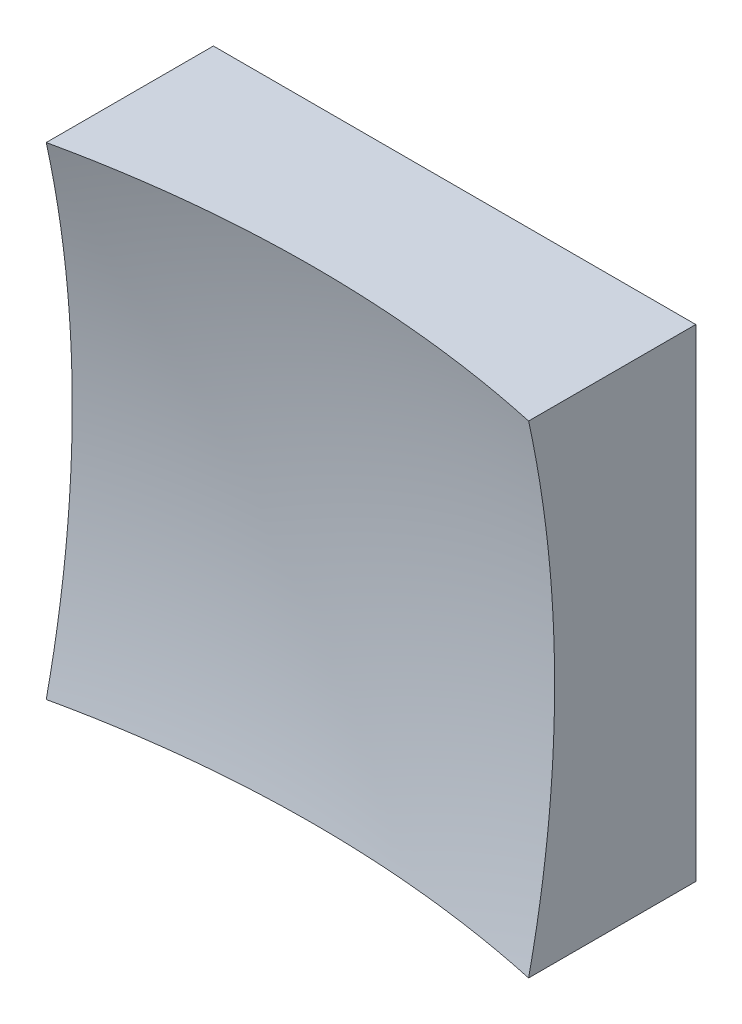
SolidWorks part; units mm, degrees
ref_plane "前视基准面" through (0, 0, 0) normal (0, 0, 1) x (1, 0, 0)
ref_plane "上视基准面" through (0, 0, 0) normal (0, 1, 0) x (1, 0, 0)
ref_plane "右视基准面" through (0, 0, 0) normal (1, 0, 0) x (0, 0, -1)
sketch "草图1" plane through (0, 0, 0) normal (0, 0, 1) x (1, 0, 0)
  line L1 (-6.25, 6.25) -> (6.25, 6.25)
  line L2 (-6.25, 6.25) -> (-6.25, -6.25)
  line L3 (-6.25, -6.25) -> (6.25, -6.25)
  line L4 (6.25, 6.25) -> (6.25, -6.25)
  line L5 (-6.25, 6.25) -> (6.25, -6.25) construction
  line L6 (-6.25, -6.25) -> (6.25, 6.25) construction
  point P0 (0, 0)
  dimension "D1" = 12.5
  dimension "D2" = 12.5
extrude "凸台-拉伸1" add sketch "草图1" along normal blind 10 contours L2 L3 L4 L1
sketch "草图2" plane through (0, 0, 0) normal (0, 1, 0) x (1, 0, 0)
  line L0 (-7.4603, -3) -> (7.3192, -3) construction
  line L1 (0, 0) -> (0, -12.1749) construction
  line L2 (29.2454, -26.3135) -> (0, -26.3135)
  line L3 (0, -26.3135) -> (0, -3)
  arc A1 (29.2454, -26.3135) -> (0, -3) centre (0, -33) ccw
  dimension "D2" = 60
  dimension "D1" = 3
revolve "切除-旋转2" cut sketch "草图2" angle 360 about L3
